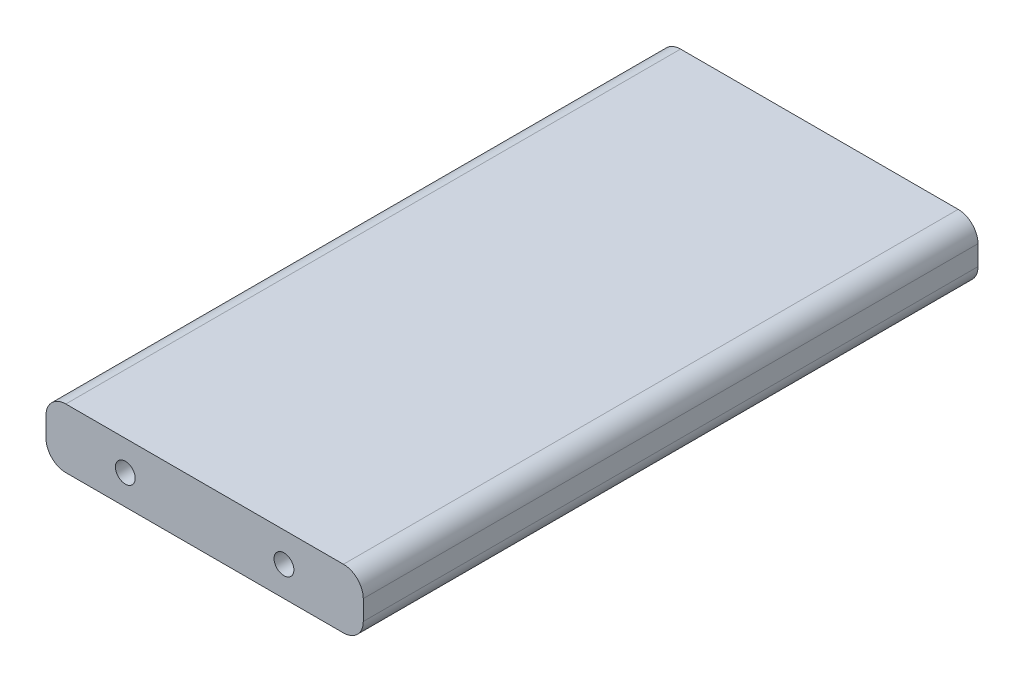
SolidWorks part; units mm, degrees
material "Mahogany"
ref_plane "Front Plane" through (0, 0, 0) normal (0, 0, 1) x (1, 0, 0)
ref_plane "Top Plane" through (0, 0, 0) normal (0, 1, 0) x (1, 0, 0)
ref_plane "Right Plane" through (0, 0, 0) normal (1, 0, 0) x (0, 0, -1)
sketch "Sketch1" plane through (0, 0, 0) normal (0, 0, 1) x (1, 0, 0)
  line L0 (44.45, 9.525) -> (50.8, 9.525)
  line L1 (-44.45, -9.525) -> (44.45, -9.525)
  line L2 (-50.8, -3.175) -> (-50.8, 3.175)
  line L3 (-44.45, 9.525) -> (44.45, 9.525)
  line L4 (50.8, -3.175) -> (50.8, 3.175)
  line L5 (-50.8, -9.525) -> (50.8, 9.525) construction
  line L6 (-50.8, 9.525) -> (50.8, -9.525) construction
  line L7 (50.8, 9.525) -> (50.8, 3.175)
  line L8 (44.45, -9.525) -> (50.8, -9.525)
  line L9 (50.8, -9.525) -> (50.8, -3.175)
  arc A2 (-50.8, -3.175) -> (-44.45, -9.525) centre (-44.45, -3.175) ccw
  arc A3 (-44.45, 9.525) -> (-50.8, 3.175) centre (-44.45, 3.175) ccw
  point P0 (0, 0)
  dimension "D1" = 19.05
  dimension "D2" = 101.6
extrude "Boss-Extrude1" add sketch "Sketch1" along normal mid plane 196.85
sketch "Sketch2" plane through (0, 0, 98.425) normal (0, 0, 1) x (1, 0, 0)
  line L0 (-25.4, -997.4935) -> (-25.4, 49002.5065) construction
  line L1 (25.4, -998.0764) -> (25.4, 49001.9236) construction
  line L2 (0, -55) -> (0, 55) construction
  line L3 (55, 0) -> (-55, 0) construction
  circle A0 centre (-25.4, 0) radius 3.175
  circle A1 centre (25.4, 0) radius 3.175
  dimension "D3" = 6.35
  dimension "D4" = 6.35
  dimension "D1" = 25.4
  dimension "D2" = 25.4
extrude "Cut-Extrude1" cut sketch "Sketch2" against normal blind 12.7
fillet "Fillet1" radius 6.35 2 edges at (50.8, -9.525, 0) (50.8, 9.525, 0)
mirror "Mirror1" about plane through (0, 0, 0) normal (0, 0, 1) of "Cut-Extrude1"
